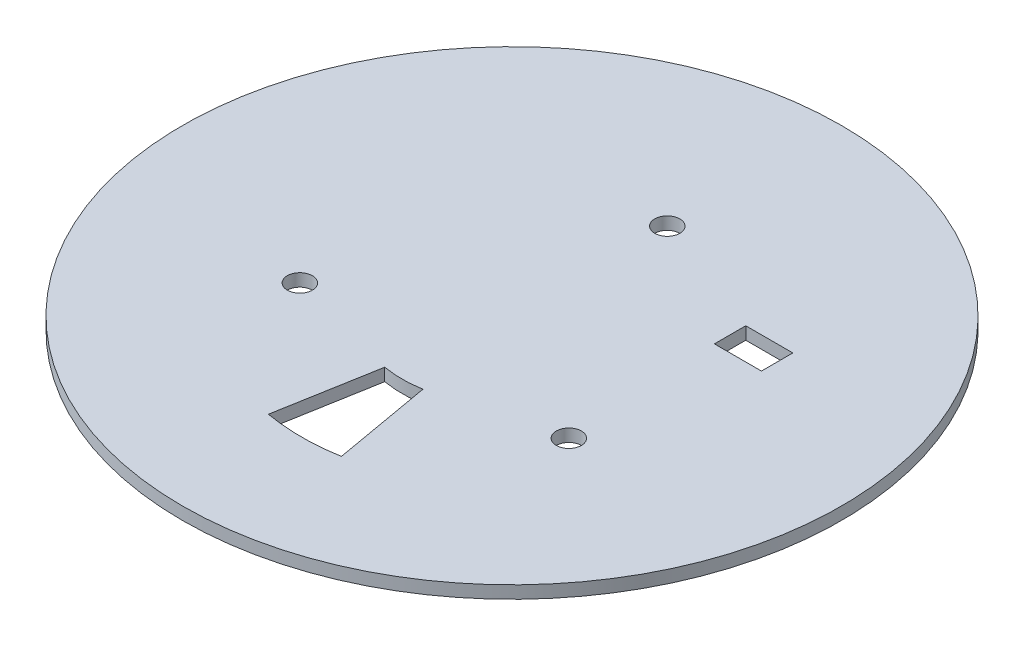
SolidWorks part; units mm, degrees
ref_plane "Plano frontal" through (0, 0, 0) normal (0, 0, 1) x (1, 0, 0)
ref_plane "Plano superior" through (0, 0, 0) normal (0, 1, 0) x (1, 0, 0)
ref_plane "Plano direito" through (0, 0, 0) normal (1, 0, 0) x (0, 0, -1)
sketch "Esboço1" plane through (0, 0, 0) normal (0, 1, 0) x (1, 0, 0)
  circle A0 centre (0, 0) radius 105
  dimension "D1" = 210
extrude "Ressalto-extrusão1" add sketch "Esboço1" along normal blind 4
sketch "Esboço2" plane through (0, 4, 0) normal (0, 1, 0) x (1, 0, 0)
  line L0 (-6.0777, -34.4683) -> (-11.6344, -65.9821) construction
  line L1 (6.0777, -34.4683) -> (11.6344, -65.9821) construction
  line L2 (-6.0777, -34.4683) -> (-11.6344, -65.9821)
  line L3 (6.0777, -34.4683) -> (11.6344, -65.9821)
  arc A0 (-11.6344, -65.9821) -> (11.6344, -65.9821) centre (0, 0) ccw construction
  arc A1 (-6.0777, -34.4683) -> (6.0777, -34.4683) centre (0, 0) ccw construction
  arc A2 (-11.6344, -65.9821) -> (11.6344, -65.9821) centre (0, 0) ccw
  arc A3 (-6.0777, -34.4683) -> (6.0777, -34.4683) centre (0, 0) ccw
extrude "Corte-extrusão1" cut sketch "Esboço2" against normal through all
sketch "Esboço3" plane through (0, 4, 0) normal (0, 1, 0) x (1, 0, 0)
  circle A0 centre (42.8509, -24.74) radius 4 construction
  circle A1 centre (0, 49.48) radius 4 construction
  circle A2 centre (-42.8509, -24.74) radius 4 construction
  circle A3 centre (42.8509, -24.74) radius 4
  circle A4 centre (0, 49.48) radius 4
  circle A5 centre (-42.8509, -24.74) radius 4
extrude "Corte-extrusão2" cut sketch "Esboço3" against normal through all
sketch "Esboço4" plane through (0, 4, 0) normal (0, 1, 0) x (1, 0, 0)
  line L0 (40, 24.48) -> (55, 24.48) construction
  line L1 (40, 34.48) -> (40, 24.48) construction
  line L2 (55, 34.48) -> (40, 34.48) construction
  line L3 (55, 24.48) -> (55, 34.48) construction
  line L4 (40, 24.48) -> (55, 24.48)
  line L5 (40, 34.48) -> (40, 24.48)
  line L6 (55, 34.48) -> (40, 34.48)
  line L7 (55, 24.48) -> (55, 34.48)
extrude "Corte-extrusão3" cut sketch "Esboço4" against normal up to next
